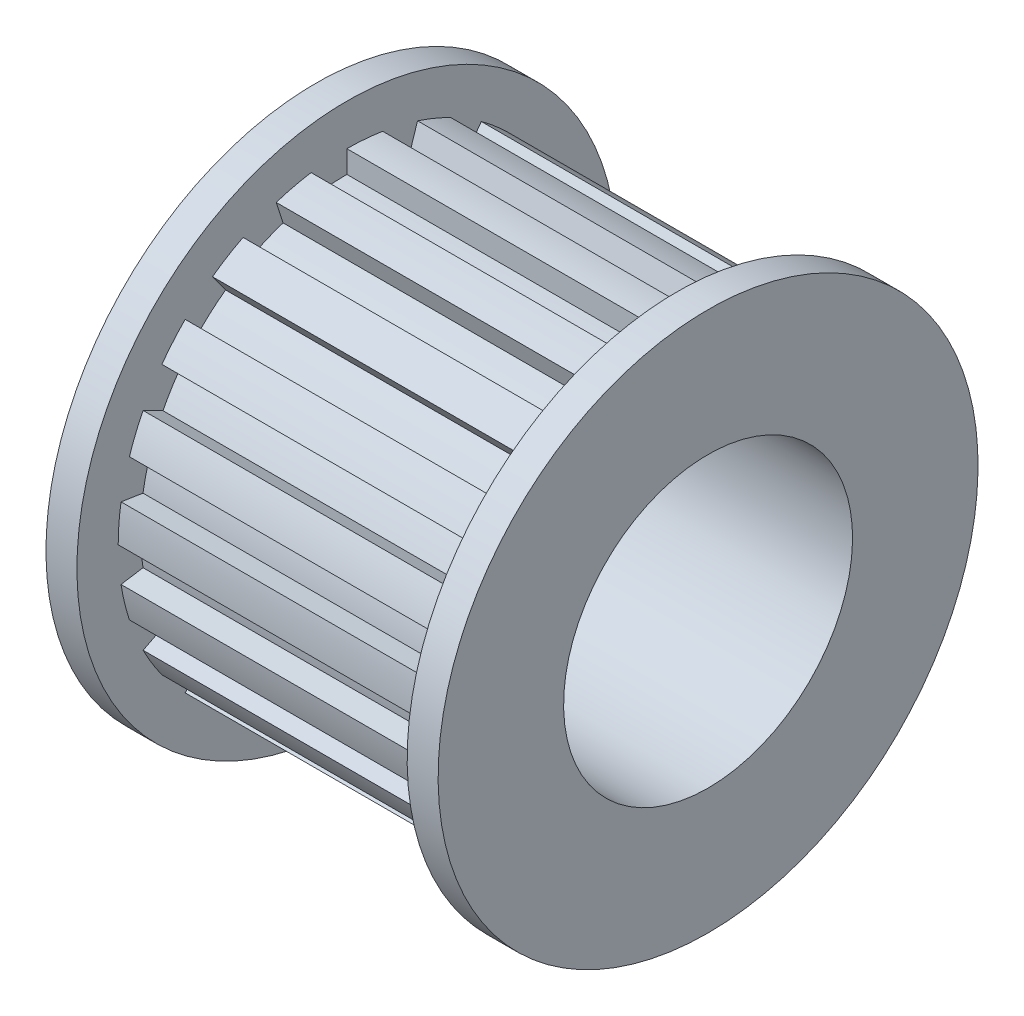
SolidWorks part; units mm, degrees
ref_plane "前视基准面" through (0, 0, 0) normal (0, 0, 1) x (1, 0, 0)
ref_plane "上视基准面" through (0, 0, 0) normal (0, 1, 0) x (1, 0, 0)
ref_plane "右视基准面" through (0, 0, 0) normal (1, 0, 0) x (0, 0, -1)
sketch "草图1" plane through (0, 0, 0) normal (0, 0, 1) x (1, 0, 0)
  line L0 (-9.5, 0) -> (9.5, 0)
  line L1 (9.5, 0) -> (9.5, 13.08)
  line L2 (9.5, 13.08) -> (8, 13.08)
  line L3 (8, 13.08) -> (8, 11.08)
  line L4 (8, 11.08) -> (-8, 11.08)
  line L5 (-8, 11.08) -> (-8, 13.08)
  line L6 (-8, 13.08) -> (-9.5, 13.08)
  line L7 (-9.5, 13.08) -> (-9.5, 0)
  line L8 (0, 27.7502) -> (0, -16.4737) construction
  dimension "D1" = 11.08
  dimension "D2" = 13.08
  dimension "D3" = 19
  dimension "D4" = 16
revolve "旋转1" add sketch "草图1" angle 360 about L0
sketch "草图2" plane through (0, 0, 0) normal (1, 0, 0) x (0, 0, -1)
  line L0 (-19.5115, 0) -> (20.7995, 0) construction
  line L1 (10, 0) -> (11.08, 0)
  line L2 (-25.2809, -4.0041) -> (25.2809, 4.0041) construction
  line L3 (9.8769, 1.5643) -> (10.9436, 1.7333)
  line L4 (9.5106, -3.0902) -> (10.5377, -3.4239)
  line L5 (9.8769, -1.5643) -> (10.9436, -1.7333)
  line L6 (8.0902, -5.8779) -> (8.9639, -6.5127)
  line L7 (8.9101, -4.5399) -> (9.8724, -5.0302)
  line L8 (5.8779, -8.0902) -> (6.5127, -8.9639)
  line L9 (7.0711, -7.0711) -> (7.8347, -7.8347)
  line L10 (3.0902, -9.5106) -> (3.4239, -10.5377)
  line L11 (4.5399, -8.9101) -> (5.0302, -9.8724)
  line L12 (0, -10) -> (0, -11.08)
  line L13 (1.5643, -9.8769) -> (1.7333, -10.9436)
  line L14 (-3.0902, -9.5106) -> (-3.4239, -10.5377)
  line L15 (-1.5643, -9.8769) -> (-1.7333, -10.9436)
  line L16 (-5.8779, -8.0902) -> (-6.5127, -8.9639)
  line L17 (-4.5399, -8.9101) -> (-5.0302, -9.8724)
  line L18 (-8.0902, -5.8779) -> (-8.9639, -6.5127)
  line L19 (-7.0711, -7.0711) -> (-7.8347, -7.8347)
  line L20 (-9.5106, -3.0902) -> (-10.5377, -3.4239)
  line L21 (-8.9101, -4.5399) -> (-9.8724, -5.0302)
  line L22 (-10, 0) -> (-11.08, 0)
  line L23 (-9.8769, -1.5643) -> (-10.9436, -1.7333)
  line L24 (-9.5106, 3.0902) -> (-10.5377, 3.4239)
  line L25 (-9.8769, 1.5643) -> (-10.9436, 1.7333)
  line L26 (-8.0902, 5.8779) -> (-8.9639, 6.5127)
  line L27 (-8.9101, 4.5399) -> (-9.8724, 5.0302)
  line L28 (-5.8779, 8.0902) -> (-6.5127, 8.9639)
  line L29 (-7.0711, 7.0711) -> (-7.8347, 7.8347)
  line L30 (-3.0902, 9.5106) -> (-3.4239, 10.5377)
  line L31 (-4.5399, 8.9101) -> (-5.0302, 9.8724)
  line L32 (0, 10) -> (0, 11.08)
  line L33 (-1.5643, 9.8769) -> (-1.7333, 10.9436)
  line L34 (3.0902, 9.5106) -> (3.4239, 10.5377)
  line L35 (1.5643, 9.8769) -> (1.7333, 10.9436)
  line L36 (5.8779, 8.0902) -> (6.5127, 8.9639)
  line L37 (4.5399, 8.9101) -> (5.0302, 9.8724)
  line L38 (8.0902, 5.8779) -> (8.9639, 6.5127)
  line L39 (7.0711, 7.0711) -> (7.8347, 7.8347)
  line L40 (9.5106, 3.0902) -> (10.5377, 3.4239)
  line L41 (8.9101, 4.5399) -> (9.8724, 5.0302)
  arc A0 (10, 0) -> (9.8769, 1.5643) centre (0, 0) ccw
  arc A2 (11.08, 0) -> (10.9436, 1.7333) centre (0, 0) ccw
  arc A3 (9.5106, -3.0902) -> (9.8769, -1.5643) centre (0, 0) ccw
  arc A4 (10.5377, -3.4239) -> (10.9436, -1.7333) centre (0, 0) ccw
  arc A5 (8.0902, -5.8779) -> (8.9101, -4.5399) centre (0, 0) ccw
  arc A6 (8.9639, -6.5127) -> (9.8724, -5.0302) centre (0, 0) ccw
  arc A7 (5.8779, -8.0902) -> (7.0711, -7.0711) centre (0, 0) ccw
  arc A8 (6.5127, -8.9639) -> (7.8347, -7.8347) centre (0, 0) ccw
  arc A9 (3.0902, -9.5106) -> (4.5399, -8.9101) centre (0, 0) ccw
  arc A10 (3.4239, -10.5377) -> (5.0302, -9.8724) centre (0, 0) ccw
  arc A11 (0, -10) -> (1.5643, -9.8769) centre (0, 0) ccw
  arc A12 (0, -11.08) -> (1.7333, -10.9436) centre (0, 0) ccw
  arc A13 (-3.0902, -9.5106) -> (-1.5643, -9.8769) centre (0, 0) ccw
  arc A14 (-3.4239, -10.5377) -> (-1.7333, -10.9436) centre (0, 0) ccw
  arc A15 (-5.8779, -8.0902) -> (-4.5399, -8.9101) centre (0, 0) ccw
  arc A16 (-6.5127, -8.9639) -> (-5.0302, -9.8724) centre (0, 0) ccw
  arc A17 (-8.0902, -5.8779) -> (-7.0711, -7.0711) centre (0, 0) ccw
  arc A18 (-8.9639, -6.5127) -> (-7.8347, -7.8347) centre (0, 0) ccw
  arc A19 (-9.5106, -3.0902) -> (-8.9101, -4.5399) centre (0, 0) ccw
  arc A20 (-10.5377, -3.4239) -> (-9.8724, -5.0302) centre (0, 0) ccw
  arc A21 (-10, 0) -> (-9.8769, -1.5643) centre (0, 0) ccw
  arc A22 (-11.08, 0) -> (-10.9436, -1.7333) centre (0, 0) ccw
  arc A23 (-9.5106, 3.0902) -> (-9.8769, 1.5643) centre (0, 0) ccw
  arc A24 (-10.5377, 3.4239) -> (-10.9436, 1.7333) centre (0, 0) ccw
  arc A25 (-8.0902, 5.8779) -> (-8.9101, 4.5399) centre (0, 0) ccw
  arc A26 (-8.9639, 6.5127) -> (-9.8724, 5.0302) centre (0, 0) ccw
  arc A27 (-5.8779, 8.0902) -> (-7.0711, 7.0711) centre (0, 0) ccw
  arc A28 (-6.5127, 8.9639) -> (-7.8347, 7.8347) centre (0, 0) ccw
  arc A29 (-3.0902, 9.5106) -> (-4.5399, 8.9101) centre (0, 0) ccw
  arc A30 (-3.4239, 10.5377) -> (-5.0302, 9.8724) centre (0, 0) ccw
  arc A31 (0, 10) -> (-1.5643, 9.8769) centre (0, 0) ccw
  arc A32 (0, 11.08) -> (-1.7333, 10.9436) centre (0, 0) ccw
  arc A33 (3.0902, 9.5106) -> (1.5643, 9.8769) centre (0, 0) ccw
  arc A34 (3.4239, 10.5377) -> (1.7333, 10.9436) centre (0, 0) ccw
  arc A35 (5.8779, 8.0902) -> (4.5399, 8.9101) centre (0, 0) ccw
  arc A36 (6.5127, 8.9639) -> (5.0302, 9.8724) centre (0, 0) ccw
  arc A37 (8.0902, 5.8779) -> (7.0711, 7.0711) centre (0, 0) ccw
  arc A38 (8.9639, 6.5127) -> (7.8347, 7.8347) centre (0, 0) ccw
  arc A39 (9.5106, 3.0902) -> (8.9101, 4.5399) centre (0, 0) ccw
  arc A40 (10.5377, 3.4239) -> (9.8724, 5.0302) centre (0, 0) ccw
  point P88 (0, 0)
  dimension "D1" = 20
  dimension "D2" = 20
  dimension "D4" = 11.08
  dimension "D3" = 9
sketch "草图7" plane through (0, 0, 0) normal (1, 0, 0) x (0, 0, -1)
  circle A0 centre (0, 0) radius 7
  dimension "D1" = 14
extrude "切除-拉伸3" cut sketch "草图7" against normal mid plane 20
extrude "切除-拉伸4" cut sketch "草图2" against normal mid plane 16
